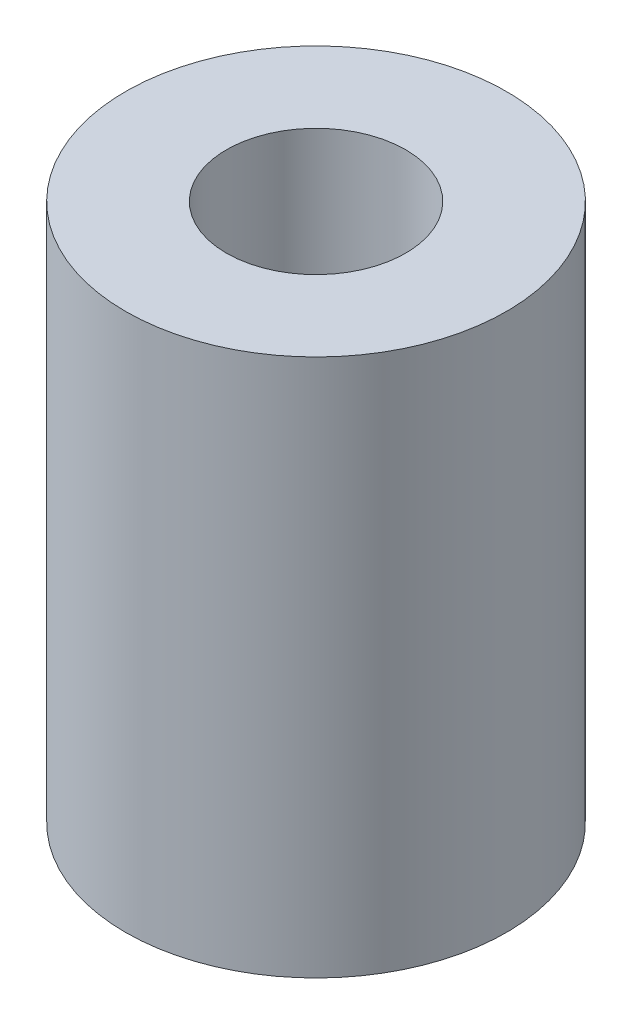
SolidWorks part; units mm, degrees
ref_plane "Front Plane" through (0, 0, 0) normal (0, 0, 1) x (1, 0, 0)
ref_plane "Top Plane" through (0, 0, 0) normal (0, 1, 0) x (1, 0, 0)
ref_plane "Right Plane" through (0, 0, 0) normal (1, 0, 0) x (0, 0, -1)
sketch "Sketch1" plane through (0, 0, 0) normal (0, 1, 0) x (1, 0, 0)
  circle A0 centre (0, 0) radius 2.125
  circle A1 centre (0, 0) radius 1
  dimension "D1" = 4.25
  dimension "D2" = 2
extrude "Boss-Extrude1" add sketch "Sketch1" along normal blind 6
